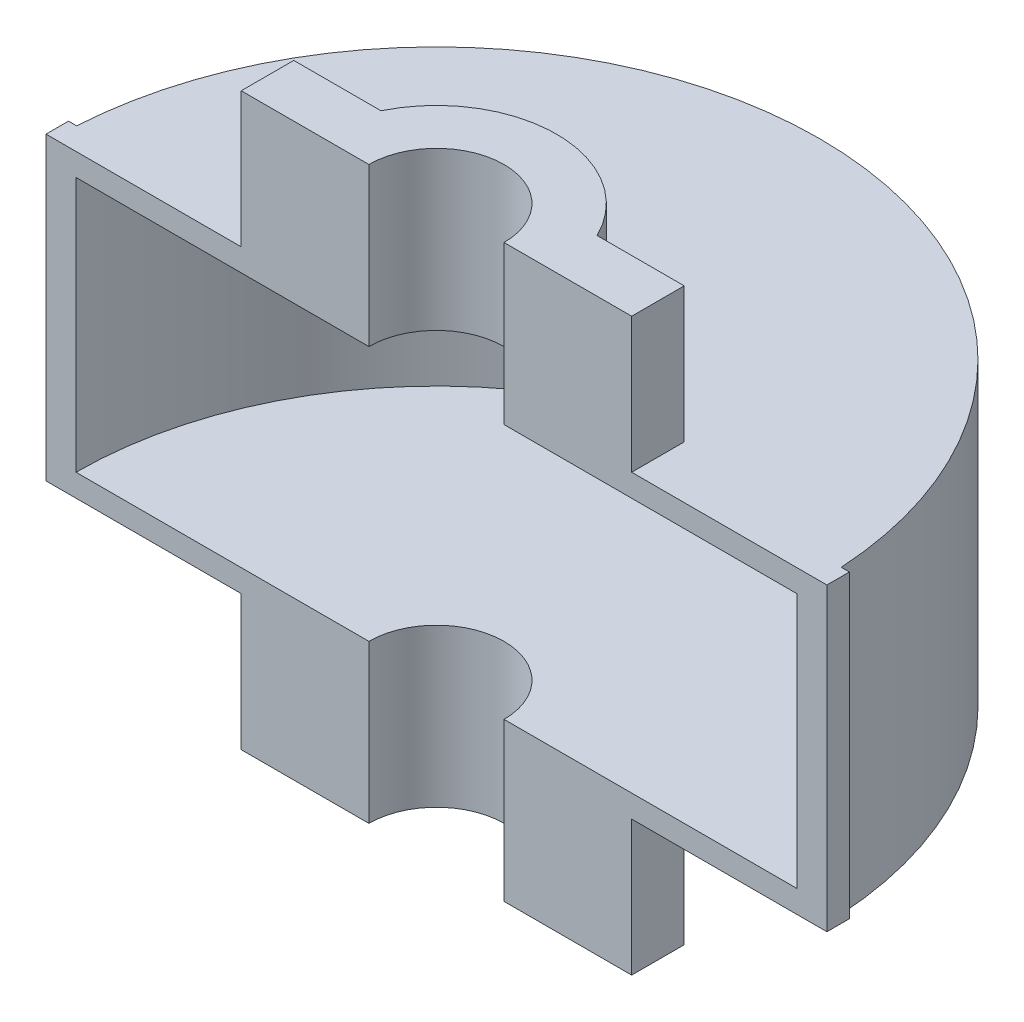
SolidWorks part; units mm, degrees
ref_plane "Front Plane" through (0, 0, 0) normal (0, 0, 1) x (1, 0, 0)
ref_plane "Top Plane" through (0, 0, 0) normal (0, 1, 0) x (1, 0, 0)
ref_plane "Right Plane" through (0, 0, 0) normal (1, 0, 0) x (0, 0, -1)
sketch "Sketch1" plane through (0, 0, 0) normal (0, 0, 1) x (1, 0, 0)
  line L0 (0, 0) -> (0, 236.218) construction
  line L2 (144, 9) -> (144, 111)
  line L3 (144, 111) -> (0, 111)
  line L4 (0, 111) -> (0, 120)
  line L5 (0, 120) -> (153, 120)
  line L6 (153, 120) -> (153, 0)
  line L9 (0, 0) -> (153, 0)
  line L10 (144, 9) -> (0, 9)
  line L11 (0, 9) -> (0, 0)
  point P4 (0, 0)
  point P9 (0, 0)
  point P10 (0, 0)
  point P12 (0, 0)
  point P13 (0, 0)
  point P14 (0, 0)
  point P15 (0, 0)
  point P16 (0, 0)
  point P17 (0, 0)
  dimension "D1" = 144
  dimension "D2" = 120
  dimension "D3" = 9
  dimension "D4" = 153
  dimension "D5" = 9
revolve "Revolve1" add sketch "Sketch1" angle 180 about L0
ref_plane "Plane8" through (156, 0, 0) normal (1, 0, 0) x (0, 0, -1)
sketch "Sketch3" plane through (156, 0, 0) normal (1, 0, 0) x (0, 0, -1)
  line L5 (0, 0) -> (153, 0) construction
  line L6 (0, 120) -> (9, 120)
  line L7 (0, 120) -> (0, 0)
  line L8 (0, 0) -> (9, 0)
  line L9 (9, 120) -> (9, 0)
  dimension "D1" = 9
extrude "Boss-Extrude3" add sketch "Sketch3" against normal up to surface (3.2649 mm away)
mirror "Mirror4" about plane through (0, 0, 0) normal (1, 0, 0) of "Boss-Extrude3"
ref_plane "Plane9" through (0, 0, -156) normal (0, 0, -1) x (-1, 0, 0)
sketch "Sketch6" plane through (0, 0, -156) normal (0, 0, -1) x (-1, 0, 0)
  line L0 (0, 0) -> (0, 120) construction
  line L1 (152.7351, 120) -> (-152.7351, 120) construction
  circle A2 centre (0, 60) radius 18
  circle A3 centre (0, 60) radius 27
extrude "Boss-Extrude4" add sketch "Sketch6" against normal up to next
sketch "Sketch7" plane through (0, 0, -156) normal (0, 0, -1) x (-1, 0, 0)
  circle A2 centre (0, 60) radius 18 construction
  circle A3 centre (0, 60) radius 18
extrude "Cut-Extrude1" cut sketch "Sketch7" against normal through all
ref_plane "Plane10" through (0, -54, 0) normal (0, 1, 0) x (1, 0, 0)
sketch "Sketch8" plane through (0, -54, 0) normal (0, 1, 0) x (1, 0, 0)
  line L0 (78, 0) -> (27, 0)
  line L1 (-27, 0) -> (-78, 0)
  line L2 (-43.1625, 21) -> (-78, 21)
  line L3 (78, 21) -> (43.1625, 21)
  line L4 (78, 21) -> (78, 0)
  line L6 (-78, 21) -> (-78, 0)
  line L7 (78, 21) -> (77.4578, 20.854) construction
  arc A1 (43.1625, 21) -> (-43.1625, 21) centre (0, 0) ccw
  arc A2 (27, 0) -> (-27, 0) centre (0, 0) ccw
  point P4 (0, 0)
  dimension "D1" = 21
  dimension "D2" = 96
  dimension "D3" = 54
  dimension "D4" = 78
extrude "Boss-Extrude5" add sketch "Sketch8" along normal up to next (54 mm away)
sketch "Sketch9" plane through (0, -54, 0) normal (0, 1, 0) x (1, 0, 0)
  arc A0 (27, 0) -> (-27, 0) centre (0, 0) ccw construction
  arc A1 (27, 0) -> (-27, 0) centre (0, 0) ccw
extrude "Cut-Extrude2" cut sketch "Sketch9" against normal through all both and the other way through all
ref_plane "Plane11" through (0, 60, 0) normal (0, 1, 0) x (1, 0, 0)
mirror "Mirror6" about plane through (0, 60, 0) normal (0, 1, 0) of "Boss-Extrude5"
sketch "Sketch13" plane through (0, 0, 0) normal (0, 1, 0) x (1, 0, 0)
  line L0 (23.9166, 41.6172) -> (-15.9031, 64.5009)
  arc A0 (43.1625, 21) -> (-43.1625, 21) centre (0, 0) ccw construction
  arc A1 (43.1625, 21) -> (-43.1625, 21) centre (0, 0) ccw construction
ref_plane "Plane13" through (23.9166, 0, -41.6172) normal (0.4983, 0, -0.867) x (-0.867, 0, -0.4983)
